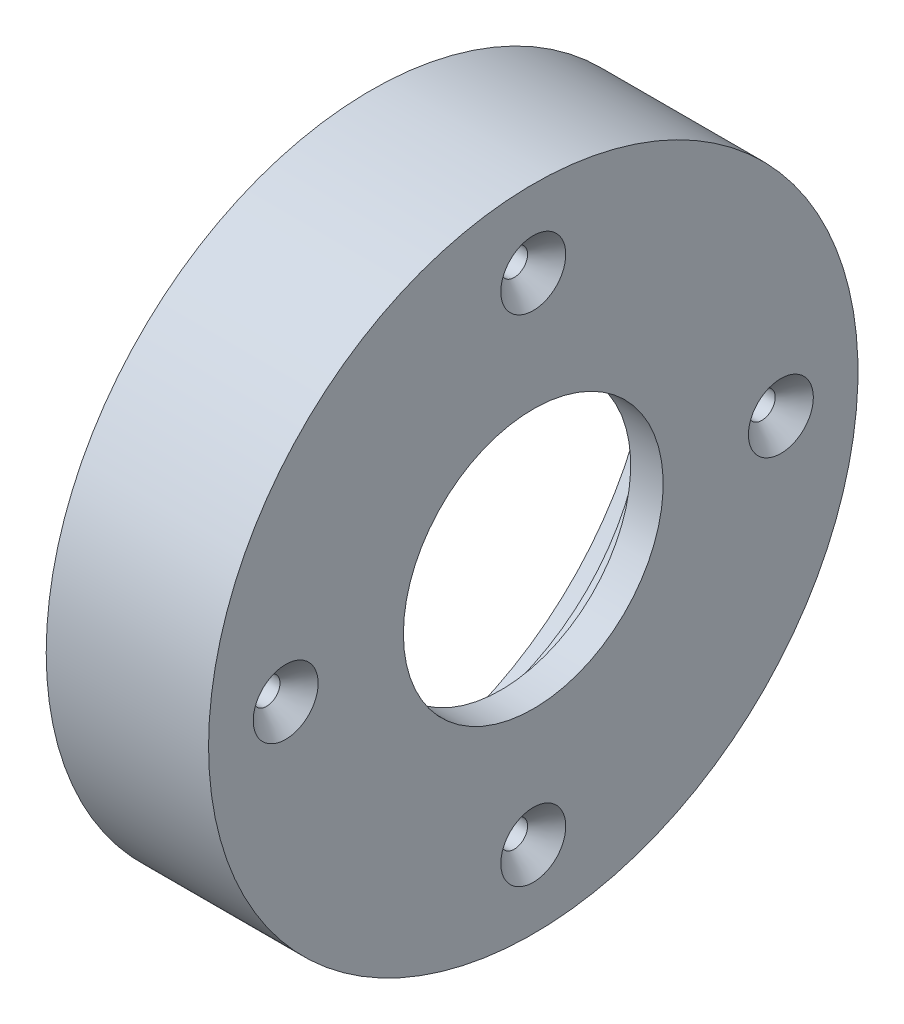
SolidWorks part; units mm, degrees
material "6061 Alloy"
ref_plane "Front Plane" through (0, 0, 0) normal (0, 0, 1) x (1, 0, 0)
ref_plane "Top Plane" through (0, 0, 0) normal (0, 1, 0) x (1, 0, 0)
ref_plane "Right Plane" through (0, 0, 0) normal (1, 0, 0) x (0, 0, -1)
sketch "Sketch2" plane through (0, 0, 0) normal (0, 0, 1) x (1, 0, 0)
  line L0 (-28.2244, 0) -> (23.6341, 0) construction
  line L1 (-14, 40) -> (6, 40)
  line L2 (0, 21) -> (2, 21)
  line L3 (0, -55) -> (0, 55) construction
  line L4 (2, 21) -> (2, 16)
  line L5 (2, 16) -> (6, 16)
  line L6 (6, 16) -> (6, 40)
  line L9 (-4, 23.5) -> (0, 23.5)
  line L10 (0, 23.5) -> (0, 21)
  line L12 (-14, 40) -> (-14, 35)
  line L13 (-14, 35) -> (-4, 35)
  line L15 (-4, 23.5) -> (-4, 35)
  dimension "D1" = 21
  dimension "D2" = 2
  dimension "D3" = 4
  dimension "D4" = 20
  dimension "D5" = 23.5
  dimension "D6" = 10
  dimension "D7" = 40
  dimension "D8" = 5
  dimension "D9" = 16
revolve "Revolve1" add sketch "Sketch2" angle 360 about L0
hole_wizard "M4x0.7 Tapped Hole1" positions "Sketch5" profile "Sketch6" tap size "M4x0.7" standard "ANSI Metric" end condition through all
sketch "Sketch5" plane through (6, 0, 0) normal (1, 0, 0) x (0, 0, -1)
  line L0 (0, 11) -> (0, -11) construction
  line L1 (11, 0) -> (-11, 0) construction
  circle A0 centre (0, 0) radius 30.5
  point P0 (0, 30.5)
  point P4 (30.5, 0)
  point P8 (0, -30.5)
  point P10 (-30.5, 0)
  dimension "D1" = 61
sketch "Sketch6" plane through (6, 30.5, 0) normal (0, 1, 0) x (0, 0, -1)
  line L0 (0, 0) -> (0, 20)
  line L1 (0, 20) -> (1.65, 20)
  line L2 (1.65, 20) -> (1.65, 2.35)
  line L3 (1.65, 2.35) -> (4, 0)
  line L5 (4, 0) -> (0, 0)
  line L6 (-1.65, 2.35) -> (-4, 0) construction
  line L11 (0, -6.35) -> (0, 107.95) construction
  dimension "Thru Tap Drill Dia." = 3.3
  dimension "Thru Tap Drill Depth" = 20
  dimension "Near C'Sink Dia." = 8
  dimension "Near C'Sink Angle" = 90
cosmetic thread "Hole Thread1" parameters "D2"=4
cosmetic thread "Hole Thread2" parameters "D2"=4
cosmetic thread "Hole Thread3" parameters "D2"=4
cosmetic thread "Hole Thread4" parameters "D2"=4
